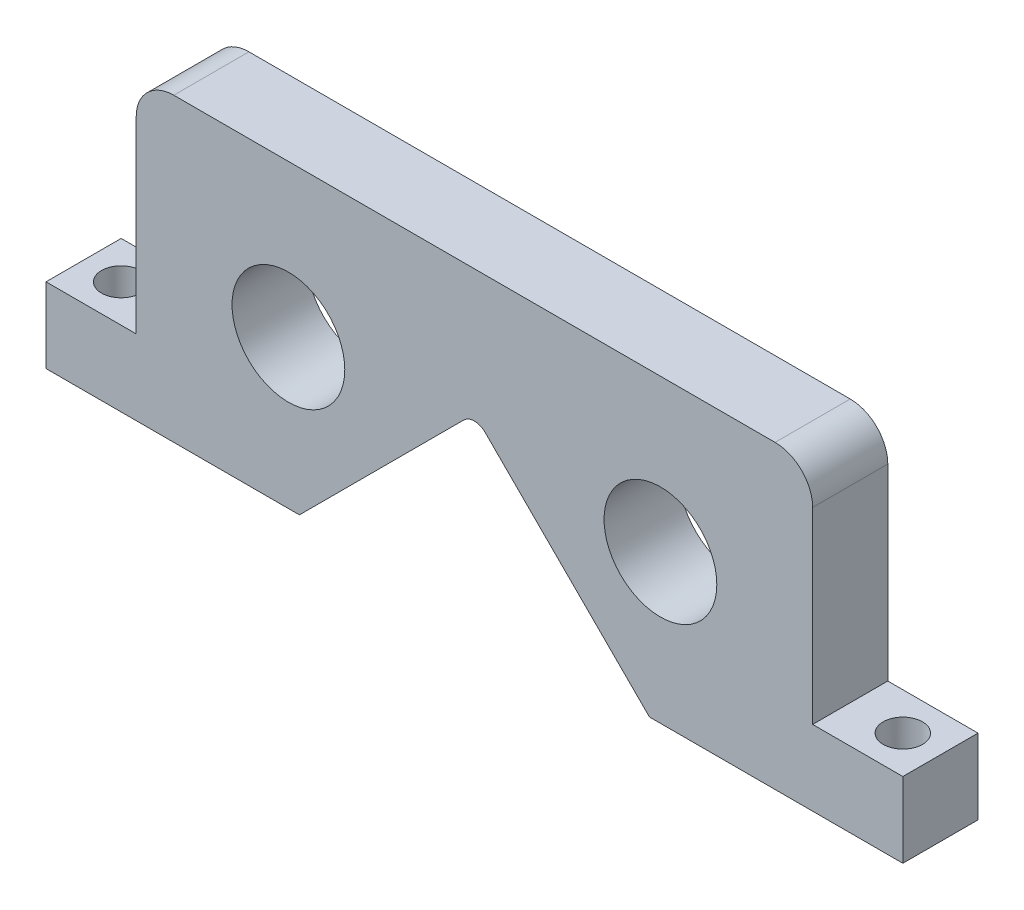
SolidWorks part; units mm, degrees
ref_plane "前基準面" through (0, 0, 0) normal (0, 0, 1) x (1, 0, 0)
ref_plane "上基準面" through (0, 0, 0) normal (0, 1, 0) x (1, 0, 0)
ref_plane "右基準面" through (0, 0, 0) normal (1, 0, 0) x (0, 0, -1)
sketch "草圖1" plane through (0, 0, 0) normal (0, 0, 1) x (1, 0, 0)
  line L0 (-57, 5) -> (57, 5)
  line L1 (40, -45) -> (-40, -45)
  line L2 (45, -40) -> (45, -10)
  line L3 (40, 45) -> (-40, 45)
  line L4 (-45, -40) -> (-45, -10)
  line L5 (45, -45) -> (-45, 45) construction
  line L6 (45, 45) -> (-45, -45) construction
  line L7 (-57, 0) -> (57, 0)
  line L8 (0, 5) -> (0, -5)
  line L9 (0, -58.0716) -> (0, 57.2128) construction
  line L10 (-1.4142, -26.8701) -> (-28.2843, 0)
  line L11 (1.4142, -26.8701) -> (28.2843, 0)
  line L12 (-28.2843, 0) -> (-1.4142, 26.8701)
  line L13 (28.2843, 0) -> (1.4142, 26.8701)
  line L14 (0, -28.2843) -> (0, 28.2843) construction
  line L15 (-28.2843, 0) -> (28.2843, 0) construction
  line L16 (-57, 15) -> (-57, 5)
  line L17 (-57, 0) -> (-57, -10)
  line L19 (-45, 40) -> (-45, 15)
  line L21 (57, 15) -> (57, 5)
  line L25 (45, -10) -> (57, -10)
  line L26 (57, 0) -> (57, -10)
  line L27 (-45, -10) -> (-57, -10)
  line L29 (-45, 15) -> (-57, 15)
  line L30 (57, 15) -> (45, 15)
  line L31 (45, 15) -> (45, 40)
  line L32 (45, 15) -> (45, 45)
  arc A0 (40, -45) -> (45, -40) centre (40, -40) ccw
  circle A1 centre (-24.7487, 24.7487) radius 7.5
  circle A2 centre (24.7487, 24.7487) radius 7.5
  arc A3 (-40, -45) -> (-45, -40) centre (-40, -40) cw
  arc A4 (45, 40) -> (40, 45) centre (40, 40) ccw
  arc A5 (-40, 45) -> (-45, 40) centre (-40, 40) ccw
  circle A6 centre (24.7487, -24.7487) radius 7.5
  circle A7 centre (-24.7487, -24.7487) radius 7.5
  arc A8 (1.4142, -26.8701) -> (-1.4142, -26.8701) centre (0, -25.4558) cw
  arc A9 (1.4142, 26.8701) -> (-1.4142, 26.8701) centre (0, 25.4558) ccw
  point P0 (0, 0)
  point P17 (0, 0)
  dimension "D6" = 10
  dimension "D9" = 10
  dimension "D11" = 12
  dimension "D8" = 15
  dimension "D12" = 40
  dimension "D7" = 15
  dimension "D13" = 2
  dimension "D15" = 5
  dimension "D2" = 90
  dimension "D3" = 5
  dimension "D4" = 40
  dimension "D5" = 40
  dimension "D10" = 10
  dimension "D14" = 90
extrude "填料-伸長1" add sketch "草圖1" along normal mid plane 10 contours A9 L13 L0 L21 L30 L31 A4 L3 A5 L19 L29 L16 L12 A1 A2
sketch "草圖2" plane through (0, 5, 0) normal (0, -1, 0) x (1, 0, 0)
  line L0 (-57, 0) -> (-20.1212, 0) construction
  line L1 (-57, 5) -> (-57, -5) construction
  line L2 (0, 10.459) -> (0, -11.7073) construction
  circle A0 centre (-52, 0) radius 2.6121
  circle A1 centre (52, 0) radius 2.6121
  dimension "D1" = 5
sketch "草圖3" plane through (0, 15, 0) normal (0, 1, 0) x (1, 0, 0)
  line L0 (-57, 0) -> (-51, 0) construction
  line L1 (-57, -5) -> (-57, 5) construction
  line L2 (-51, 0) -> (-51, -5) construction
  line L3 (-45, -5) -> (-57, -5) construction
  line L4 (51, -5) -> (51, 0) construction
  line L5 (57, -5) -> (45, -5) construction
  line L6 (51, 0) -> (57, 0) construction
  line L7 (57, -5) -> (57, 5) construction
  circle A0 centre (-51, 0) radius 3
  circle A1 centre (51, 0) radius 3
  dimension "D1" = 6
extrude "除料-伸長1" cut sketch "草圖2" against normal through all
